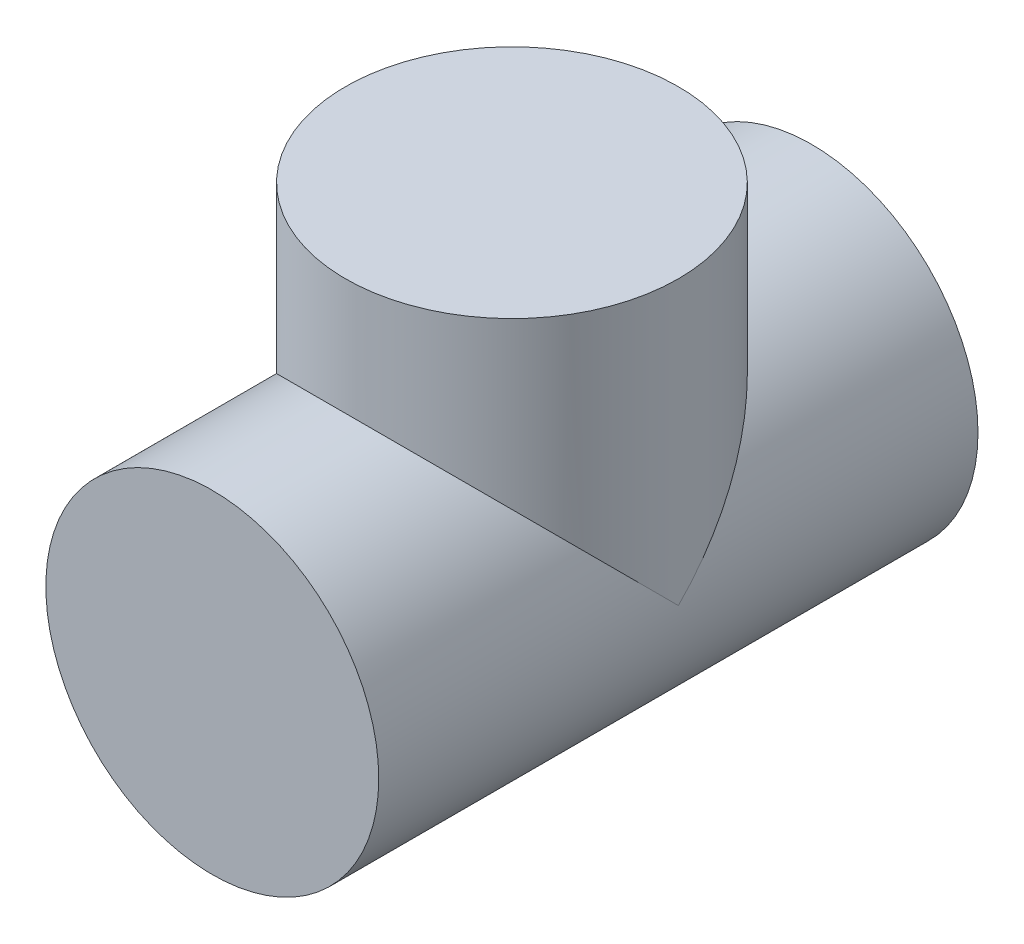
SolidWorks part; units mm, degrees
ref_plane "Front Plane" through (0, 0, 0) normal (0, 0, 1) x (1, 0, 0)
ref_plane "Top Plane" through (0, 0, 0) normal (0, 1, 0) x (1, 0, 0)
ref_plane "Right Plane" through (0, 0, 0) normal (1, 0, 0) x (0, 0, -1)
sketch "Sketch1" plane through (0, 0, 0) normal (1, 0, 0) x (0, 0, -1)
  line L0 (-45, 0) -> (45, 0)
  line L1 (45, 0) -> (45, 85)
  dimension "D1" = 90
  dimension "D2" = 85
ref_plane "Plane1" through (0, 0, 45) normal (0, 0, 1) x (1, 0, 0)
sketch "Sketch2" plane through (0, 0, 45) normal (0, 0, 1) x (1, 0, 0)
  circle A0 centre (0, 0) radius 50
  dimension "D1" = 100
sweep "Sweep1" add profiles "Sketch2" path "Sketch1"
ref_plane "Plane2" through (0, 0, -50) normal (0, 0, 1) x (1, 0, 0)
ref_plane "Plane4" through (0, 0, -45) normal (0, 0, 1) x (1, 0, 0)
mirror "Mirror2" about plane through (0, 0, -45) normal (0, 0, 1) of "Sweep1"
